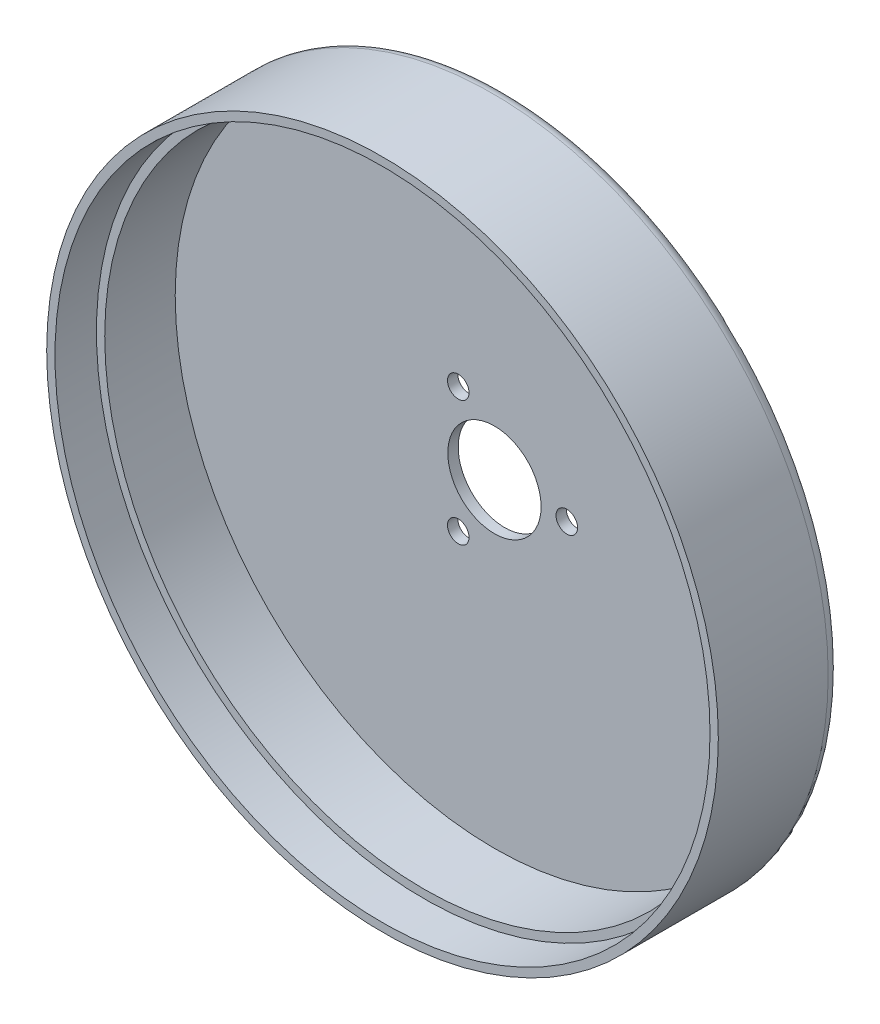
SolidWorks part; units mm, degrees
ref_plane "Front Plane" through (0, 0, 0) normal (0, 0, 1) x (1, 0, 0)
ref_plane "Top Plane" through (0, 0, 0) normal (0, 1, 0) x (1, 0, 0)
ref_plane "Right Plane" through (0, 0, 0) normal (1, 0, 0) x (0, 0, -1)
sketch "Sketch1" plane through (0, 0, 0) normal (0, 0, 1) x (1, 0, 0)
  circle A0 centre (0, 0) radius 81
  dimension "D1" = 162
extrude "Boss-Extrude1" add sketch "Sketch1" along normal blind 2.5
sketch "Sketch2" plane through (0, 0, 2.5) normal (0, 0, 1) x (1, 0, 0)
  circle A0 centre (0, 0) radius 11.25
  dimension "D1" = 22.5
extrude "Cut-Extrude1" cut sketch "Sketch2" against normal through all
sketch "Sketch3" plane through (0, 0, 2.5) normal (0, 0, 1) x (1, 0, 0)
  line L0 (-104.6653, 0) -> (111.2912, 0) construction
  line L1 (0, 113.7286) -> (0, -111.4545) construction
  line L2 (-8.725, 15.1121) -> (0, 0) construction
  line L3 (0, 0) -> (-8.725, -15.1121) construction
  circle A0 centre (0, 0) radius 17.45
  circle A1 centre (17.45, 0) radius 2.6
  circle A2 centre (-8.725, 15.1121) radius 2.6
  circle A3 centre (-8.725, -15.1121) radius 2.6
  dimension "D1" = 34.9
  dimension "D4" = 5.2
  dimension "D2" = 60
  dimension "D3" = 60
extrude "Cut-Extrude2" cut sketch "Sketch3" against normal through all contours A0 A2 | A0 A2 | A0 A1 | A0 A1 | A0 A3 | A0 A3
sketch "Sketch4" plane through (0, 0, 2.5) normal (0, 0, 1) x (1, 0, 0)
  circle A0 centre (0, 0) radius 81
  circle A1 centre (0, 0) radius 77
  dimension "D1" = 162
  dimension "D2" = 154
extrude "Boss-Extrude2" add sketch "Sketch4" along normal blind 27
sketch "Sketch5" plane through (0, 0, 29.5) normal (0, 0, 1) x (1, 0, 0)
  circle A0 centre (0, 0) radius 79
  dimension "D1" = 158
extrude "Cut-Extrude3" cut sketch "Sketch5" against normal blind 10
fillet "Fillet1" radius 3 1 edges at (81, 0, 0)
